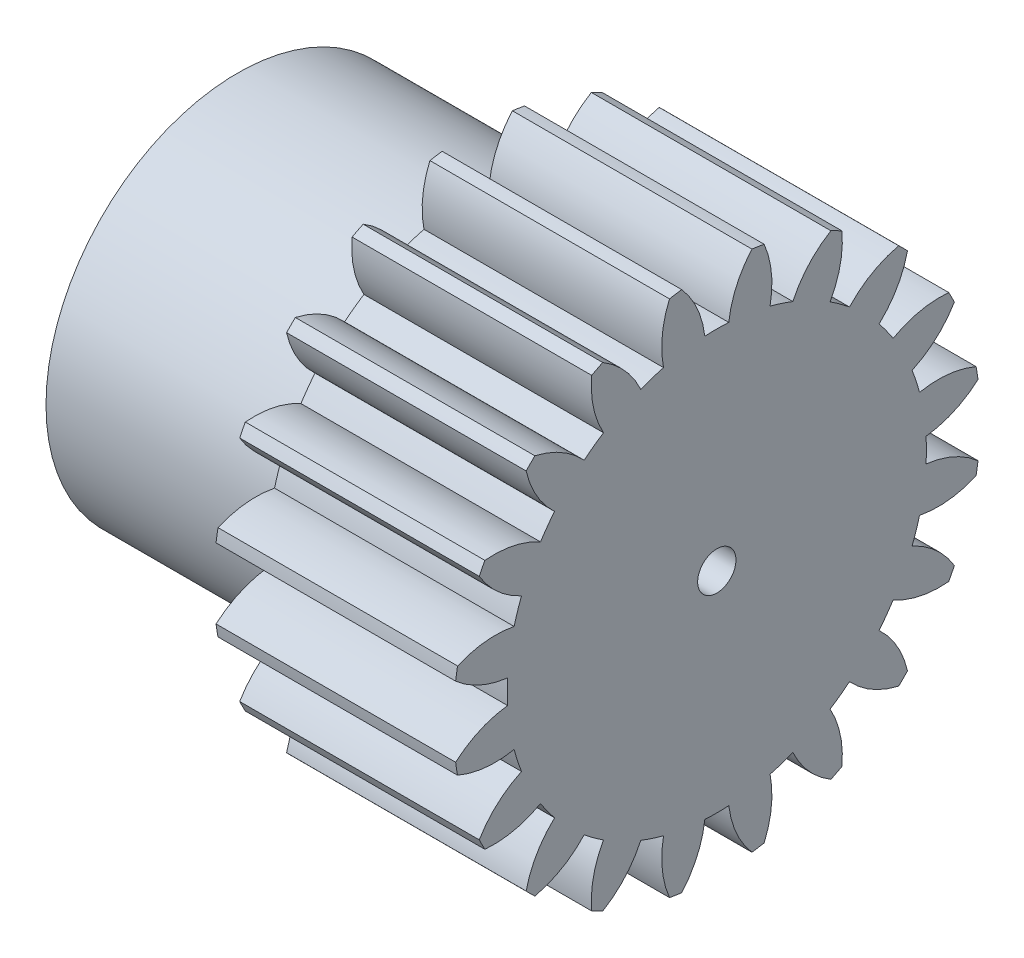
SolidWorks part; units mm, degrees
ref_plane "Plane1" through (0, 0, 0) normal (0, 0, 1) x (1, 0, 0)
ref_plane "Plane2" through (0, 0, 0) normal (0, 1, 0) x (1, 0, 0)
ref_plane "Plane3" through (0, 0, 0) normal (1, 0, 0) x (0, 0, -1)
sketch "HoldingSke" plane through (0, 0, 0) normal (0, 1, 0) x (1, 0, 0)
  line L0 (0, 0) -> (1.8794, -0.684)
  line L1 (-15, 0) -> (100, 0) construction
  line L2 (0, 0) -> (-2.1039, 2.3779)
  line L3 (0, 0) -> (-11.863, 4.5341)
  line L4 (0, 0) -> (8.1152, 2.9537)
  line L5 (0, 0) -> (-9.3695, -3.4946)
  line L6 (0, 0) -> (-4.1448, -2.7965)
  line L7 (-2.1039, 2.3779) -> (0.0486, 12.1435)
  line L8 (-76.2, 54.61) -> (-76.1, 54.61)
  line L9 (-71.009, 38.7566) -> (-53.1078, 45.2721)
  line L10 (-76.2, 71.12) -> (104.1128, 71.12)
  line L11 (0, 0) -> (-5, 0)
  line L12 (-76.2, 101.6) -> (-76.181, 101.6)
  line L13 (24.9733, 27.94) -> (52.9518, 28.4284)
  line L14 (24.9733, 27.94) -> (24.9743, 27.94)
  line L15 (24.9733, 27.94) -> (100.4006, 29.5858)
  line L16 (-63.627, -0.5) -> (-12.827, -0.5)
  circle A0 centre (0, 0) radius 0.4
  circle A1 centre (0, 0) radius 4
  circle A2 centre (0, 0) radius 4
  circle A3 centre (0, 0) radius 0.4
  dimension "MHD" = 8
  dimension "Hub_dia" = 8
  dimension "Bore" = 0.8
  dimension "MBD" = 0.8
  dimension "Num_teeth" = 20
  dimension "Pitch" = 2
  dimension "Overall_len" = 10
  dimension "Show_teeth" = 20
  dimension "Thickness" = 5
  dimension "OAL" = 10.0001
  dimension "T_dim" = 0.1
  dimension "Ap" = 20
  dimension "H" = 19.05
  dimension "Pitch_radius" = 180.3128
  dimension "Width" = 5
  dimension "Backlash" = 0.019
  dimension "Addendum_fac" = 1
  dimension "Dedendum_fac" = 1.25
  dimension "Clearance_fac" = 0.25
  dimension "Dedendum_add" = 0.001
  dimension "Module" = 0.5
sketch "BasProSke" plane through (0, 0, 0) normal (0, 1, 0) x (1, 0, 0)
  line L0 (-10, 0) -> (60, 0) construction
  line L1 (0, 0) -> (0, 5.5)
  line L2 (0, 0) -> (5, 0)
  line L3 (5, 0) -> (5, 5.5)
  line L4 (5, 5.5) -> (0, 5.5)
  dimension "Thickness" = 5
  dimension "Diameter" = 11
revolve "Base-Revolve" add sketch "BasProSke" angle 360 about L0
sketch "TooCutSke" plane through (0, 0, 0) normal (1, 0, 0) x (0, 0, -1)
  line L1 (0, 0) -> (0, 107) construction
  line L2 (0, 0) -> (-0.4255, 4.9819) construction
  line L3 (0, 0) -> (-1.5603, 9.8514) construction
  line L4 (-0.4255, 4.9819) -> (-0.7802, 4.9257) construction
  arc A0 (0.2499, 4.3669) -> (-0.2499, 4.3669) centre (0, 0) ccw
  arc A1 (0.7528, 5.4739) -> (-0.7528, 5.4739) centre (0, 0) ccw
  circle A2 centre (0, 0) radius 5 construction
  circle A3 centre (0, 0) radius 4.6985 construction
  arc A4 (-0.2499, 4.3669) -> (-0.7528, 5.4739) centre (-2.2361, 4.1322) ccw
  arc A5 (0.7528, 5.4739) -> (0.2499, 4.3669) centre (2.2361, 4.1322) ccw
  dimension "Root_dia" = 8.748
  dimension "Overcut_dia" = 11.0508
  dimension "Pitch_dia" = 10
  dimension "Base_dia" = 9.3969
  dimension "Flank_rad" = 2
  dimension "Half_ang" = 9
  dimension "Half_CT" = 0.359
extrude "ToothCut" cut sketch "TooCutSke" along normal through all
fillet "Breaks" [suppressed] radius 0.01
fillet "RootFillets" [suppressed] radius 0.126
pattern_circular "TeethCuts" count 20 every 18 about axis through (-10, 0, 0) along (1, 0, 0) of "ToothCut", "RootFillets", "Breaks"
sketch "HubNeaOneSke" plane through (0, 0, 0) normal (-1, 0, 0) x (0, 0, 1)
  circle A0 centre (0, 0) radius 4
  dimension "Diameter" = 8
extrude "HubNearOne" add sketch "HubNeaOneSke" along normal blind 5.0001
sketch "HubNeaBotSke" plane through (0, 0, 0) normal (-1, 0, 0) x (0, 0, 1)
  circle A0 centre (0, 0) radius 4
  dimension "Diameter" = 8
extrude "HubNearBoth" [suppressed] add sketch "HubNeaBotSke" along normal blind 2.5
ref_plane "FarPln" through (5, 0, 0) normal (1, 0, 0) x (0, 0, -1)
sketch "HubFarSke" plane through (5, 0, 0) normal (1, 0, 0) x (0, 0, -1)
  circle A0 centre (0, 0) radius 4
  dimension "Diameter" = 8
extrude "HubFar" [suppressed] add sketch "HubFarSke" along normal blind 2.5
sketch "BorSke" plane through (0, 0, 0) normal (1, 0, 0) x (0, 0, -1)
  circle A0 centre (0, 0) radius 0.4
  dimension "Diameter" = 0.8
extrude "Bore" cut sketch "BorSke" along normal mid plane 20.0001
sketch "KeySke" plane through (0, 0, 0) normal (1, 0, 0) x (0, 0, -1)
  line L0 (-0.05, 0) -> (-0.05, 0.5)
  line L1 (-0.05, 0.5) -> (0.05, 0.5)
  line L2 (0.05, 0.5) -> (0.05, 0)
  line L3 (0, 0) -> (0, 34) construction
  line L4 (-0.05, 0) -> (0.05, 0)
  dimension "Offset" = 0.5
  dimension "Width" = 0.1
extrude "Keyway" [suppressed] cut sketch "KeySke" along normal mid plane 20.0001
pattern_circular "Keyway2" [suppressed] count 2 every 90 about axis through (-10, 0, 0) along (1, 0, 0)
equation "' \"Module@HoldingSke\" = 6.35"
equation "' \"Num_teeth@HoldingSke\" = 12"
equation "' \"Ap@HoldingSke\" =  20"
equation "' \"Ap@HoldingSke\" = 20"
equation "' \"Width@HoldingSke\" = 0.5 * 25.4"
equation "' \"Hub_dia@HoldingSke\"= 1 * 25.4"
equation "' \"Hub_dia@HoldingSke\" = 1 * 25.4"
equation "' \"Overall_len@HoldingSke\" = 1.0 * 25.4"
equation "' \"Bore@HoldingSke\" = 0.75 * 25.4"
equation "' \"T_dim@HoldingSke\" = 0.1 * 25.4"
equation "' \"Width@KeySke\" = 0.25 * 25.4"
equation "' \"Show_teeth@HoldingSke\" = 13"
equation "' \"Backlash@HoldingSke\" = 0.009 * 25.4"
equation "' \"Addendum_fac@HoldingSke\" = 1.0"
equation "' \"Dedendum_fac@HoldingSke\" = 1.25"
equation "' \"Dedendum_add@HoldingSke\" = 0.00005 * 25.4"
equation "' \"Clearance_fac@HoldingSke\" = 0.25"
equation "\"Pitch@HoldingSke\" = 1 / \"Module@HoldingSke\""
equation "\"Overcut_dia@TooCutSke\" = (\"Num_teeth@HoldingSke\" + 2 * \"Addendum_fac@HoldingSke\") / \"Pitch@HoldingSke\" + 0.002 * 25.4"
equation "\"Pitch_dia@TooCutSke\" = \"Num_teeth@HoldingSke\" / \"Pitch@HoldingSke\""
equation "\"Base_dia@TooCutSke\" = \"Num_teeth@HoldingSke\" / \"Pitch@HoldingSke\" * cos((\"Ap@HoldingSke\"  * 3.14159265 / 180))"
equation "\"Root_dia@TooCutSke\" = (\"Num_teeth@HoldingSke\" + 2) / \"Pitch@HoldingSke\" - 2 * (\"Addendum_fac@HoldingSke\" + \"Dedendum_fac@HoldingSke\") / \"Pitch@HoldingSke\" - \"Dedendum_add@HoldingSke\" * 2"
equation "\"Half_ang@TooCutSke\" = 180 / \"Num_teeth@HoldingSke\""
equation "\"Half_CT@TooCutSke\" = \"Num_teeth@HoldingSke\" / \"Pitch@HoldingSke\" * sin((3.14159265 / 2 / \"Num_teeth@HoldingSke\")) / 2 - 7 * \"Backlash@HoldingSke\" / 4"
equation "\"Flank_rad@TooCutSke\" = \"Num_teeth@HoldingSke\" / \"Pitch@HoldingSke\" / 5"
equation "\"Radius@RootFillets\" = \"Clearance_fac@HoldingSke\" / \"Pitch@HoldingSke\" + \"Dedendum_add@HoldingSke\""
equation "\"Break_rad@Breaks\" = 0.02 / \"Pitch@HoldingSke\""
equation "\"Thickness@HoldingSke\" = \"Width@HoldingSke\""
equation "\"OAL@HoldingSke\" = \"Thickness@HoldingSke\""
equation "\"MHD@HoldingSke\" = (\"Num_teeth@HoldingSke\" + 2) / \"Pitch@HoldingSke\" - 2 * (\"Addendum_fac@HoldingSke\" + \"Dedendum_fac@HoldingSke\")  / \"Pitch@HoldingSke\" - \"Dedendum_add@HoldingSke\" * 2"
equation "\"MBD@HoldingSke\" = (\"Num_teeth@HoldingSke\" + 2) / \"Pitch@HoldingSke\" - 2 * (\"Addendum_fac@HoldingSke\" + \"Dedendum_fac@HoldingSke\")  / \"Pitch@HoldingSke\" - \"Dedendum_add@HoldingSke\" * 2 - 0.002 * 25.4"
equation "\"MHD@HoldingSke\" = ((sgn( \"MHD@HoldingSke\" - \"Hub_dia@HoldingSke\" )-1)*( \"MHD@HoldingSke\" - \"Hub_dia@HoldingSke\" ))/-2+ \"Hub_dia@HoldingSke\""
equation "\"MBD@HoldingSke\" = ((sgn( \"MBD@HoldingSke\" - \"Bore@HoldingSke\" )-1)*( \"MBD@HoldingSke\" - \"Bore@HoldingSke\" ))/-2+ \"Bore@HoldingSke\""
equation "\"OAL@HoldingSke\" = ((sgn( \"OAL@HoldingSke\" - \"Overall_len@HoldingSke\" )+1)*( \"OAL@HoldingSke\" - \"Overall_len@HoldingSke\" ))/2 + \"Overall_len@HoldingSke\" + 0.000002 * 25.4"
equation "\"Num_teeth@TeethCuts\" = int( \"Show_teeth@HoldingSke\" ) + 1"
equation "\"Num_teeth@TeethCuts\" = ((sgn( \"Num_teeth@TeethCuts\" - \"Num_teeth@HoldingSke\" )-1)*( \"Num_teeth@TeethCuts\" - \"Num_teeth@HoldingSke\" ))/-2+ \"Num_teeth@HoldingSke\""
equation "\"Num_teeth@TeethCuts\" = ((sgn( \"Num_teeth@TeethCuts\" - 2.0)+1)*( \"Num_teeth@TeethCuts\" - 2.0))/2 +2.0"
equation "\"Angle@TeethCuts\" = 360.0 / \"Num_teeth@HoldingSke\""
equation "\"Diameter@BasProSke\" = (\"Num_teeth@HoldingSke\" + 2 * \"Addendum_fac@HoldingSke\") / \"Pitch@HoldingSke\""
equation "\"Thickness@BasProSke\"  = \"Thickness@HoldingSke\""
equation "' \"Fillet_rad@BasProSke\" =  \"Thickness@HoldingSke\" * 0.05"
equation "' \"Fillet_rad@BasProSke\" = \"Thickness@HoldingSke\" * 0.05"
equation "\"MHD@HoldingSke\" = ((sgn( \"MHD@HoldingSke\" - \"Root_dia@TooCutSke\" )-1)*( \"MHD@HoldingSke\" - \"Root_dia@TooCutSke\" ))/-2+ \"Root_dia@TooCutSke\""
equation "\"Diameter@HubNeaOneSke\" = \"MHD@HoldingSke\""
equation "\"Length@HubNearOne\" = \"OAL@HoldingSke\" - \"Thickness@BasProSke\""
equation "\"Diameter@HubNeaBotSke\" = \"MHD@HoldingSke\""
equation "\"Length@HubNearBoth\" = ( \"OAL@HoldingSke\" - \"Thickness@BasProSke\" ) / 2.0"
equation "\"Thickness@FarPln\" = \"Thickness@BasProSke\""
equation "\"Diameter@HubFarSke\" = \"MHD@HoldingSke\""
equation "\"Length@HubFar\" = ( \"OAL@HoldingSke\" - \"Thickness@BasProSke\" ) / 2.0"
equation "\"Diameter@BorSke\" = \"MBD@HoldingSke\""
equation "\"D1@Bore\" = \"OAL@HoldingSke\" * 2.0"
equation "\"D1@Keyway\" = \"OAL@HoldingSke\" * 2.0"
equation "\"Offset@KeySke\" = \"T_dim@HoldingSke\" + \"MBD@HoldingSke\" / 2.0"
